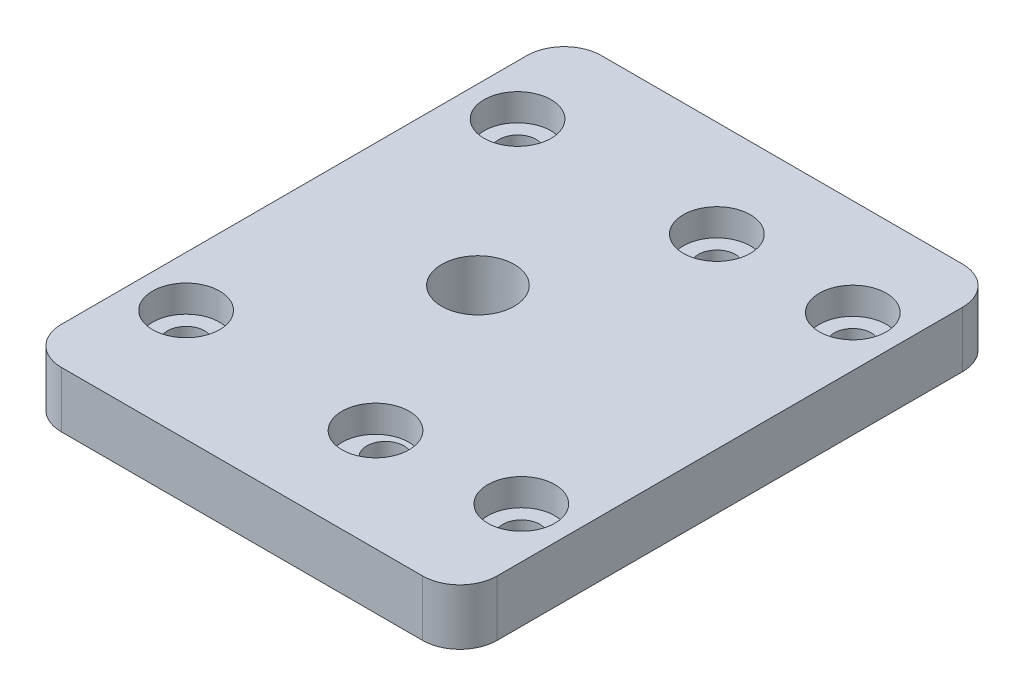
SolidWorks part; units mm, degrees
material "Custom Plastic"
ref_plane "Front Plane" through (0, 0, 0) normal (0, 0, 1) x (1, 0, 0)
ref_plane "Top Plane" through (0, 0, 0) normal (0, 1, 0) x (1, 0, 0)
ref_plane "Right Plane" through (0, 0, 0) normal (1, 0, 0) x (0, 0, -1)
sketch "Sketch1" plane through (0, 0, 0) normal (0, 1, 0) x (1, 0, 0)
  line L0 (-30.4611, 0) -> (33.997, 0) construction
  line L1 (-11.7, -14.5) -> (11.7, -14.5)
  line L2 (-11.7, -14.5) -> (-11.7, 14.5)
  line L3 (-11.7, 14.5) -> (11.7, 14.5)
  line L4 (11.7, -14.5) -> (11.7, 14.5)
  line L5 (-11.7, -14.5) -> (11.7, 14.5) construction
  line L6 (-11.7, 14.5) -> (11.7, -14.5) construction
  circle A0 centre (9, 9.3) radius 1
  circle A2 centre (9, -8.5) radius 1
  circle A3 centre (-9, -8.5) radius 1
  circle A5 centre (1.7, -8.5) radius 1
  point P0 (0, 0)
  point P6 (-9, 8.5)
  point P7 (9, 8.5)
  point P8 (9, 9.3)
  point P18 (1.7, 8.5)
  dimension "D7" = 17.8
  dimension "D8" = 18
  dimension "D10" = 2
  dimension "D1" = 29
  dimension "D2" = 23.4
  dimension "D3" = 6
  dimension "D4" = 6
  dimension "D5" = 18
  dimension "D6" = 2.7
  dimension "D9" = 10.7
extrude "Boss-Extrude1" add sketch "Sketch1" along normal blind 3
fillet "Fillet1" radius 2 4 edges at (11.7, 1.5, -14.5) (11.7, 1.5, 14.5) (-11.7, 1.5, 14.5) (-11.7, 1.5, -14.5)
sketch "Sketch8" plane through (0, 3, 0) normal (0, 1, 0) x (1, 0, 0)
  line L0 (24.633, 0) -> (-21.7502, 0) construction
  line L1 (1.7, -8.5) -> (1.7, 20.7764) construction
  line L2 (-9, -8.5) -> (-9, 21.3011) construction
  line L3 (9, -8.5) -> (9, 9.3) construction
  line L4 (14.3582, 9.3) -> (-23.7207, 9.3) construction
  circle A0 centre (1.7, 9.3) radius 1
  circle A1 centre (-9, 9.3) radius 1
  point P15 (1.7, 9.3)
  point P16 (-9, 9.3)
  dimension "D1" = 2
  dimension "D2" = 2
extrude "Cut-Extrude5" cut sketch "Sketch8" against normal blind 10
sketch "Sketch10" plane through (0, 3, 0) normal (0, 1, 0) x (1, 0, 0)
  line L1 (9.7, 14.5) -> (-9.7, 14.5) construction
  circle A1 centre (-2.3282, 0.5) radius 1.5 construction
  circle A2 centre (-2.3282, 0.5) radius 1.95
  dimension "D1" = 3.9
  dimension "D2" = 14
extrude "Cut-Extrude6" cut sketch "Sketch10" against normal blind 10
sketch "Sketch11" plane through (0, 3, 0) normal (0, 1, 0) x (1, 0, 0)
  circle A0 centre (-9, -8.5) radius 1.8
  circle A1 centre (1.6718, -9) radius 1.8
  circle A2 centre (9, -8.5) radius 1.8
  circle A3 centre (9, 9.3) radius 1.8
  circle A4 centre (1.7, 9.3) radius 1.8
  circle A5 centre (-9, 9.3) radius 1.8
  dimension "D1" = 3.6
  dimension "D2" = 3.6
  dimension "D3" = 3.6
  dimension "D4" = 3.6
  dimension "D5" = 3.6
  dimension "D6" = 3.6
extrude "Cut-Extrude7" cut sketch "Sketch11" against normal blind 1.45
